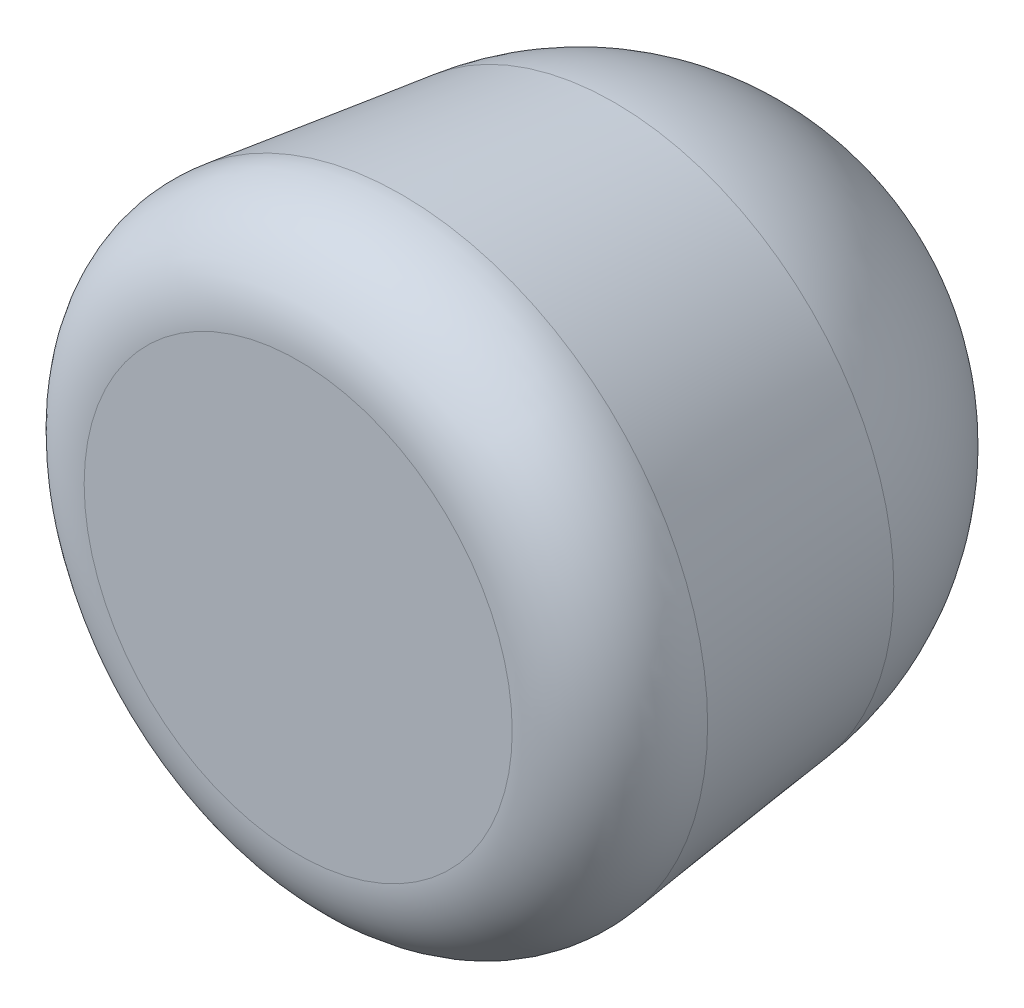
SolidWorks part; units mm, degrees
ref_plane "Front" through (0, 0, 0) normal (0, 0, 1) x (1, 0, 0)
ref_plane "Top" through (0, 0, 0) normal (0, 1, 0) x (1, 0, 0)
ref_plane "Right" through (0, 0, 0) normal (1, 0, 0) x (0, 0, -1)
sketch "Sketch1" plane through (0, 0, 0) normal (1, 0, 0) x (0, 0, -1)
  line L0 (18.6976, 151.2487) -> (-96.2656, 165.4606)
  line L1 (-152.4, 115.8383) -> (-152.4, 0)
  line L2 (0, 0) -> (152.4, 0) construction
  line L3 (152.4, 0) -> (-152.4, 0)
  arc A0 (-96.2656, 165.4606) -> (-152.4, 115.8383) centre (-102.4, 115.8383) ccw
  ellipse E0 centre (0, 0) end of major axis (0, 152.4) minor radius 152.4 (152.4, 0) -> (-152.4, 0) ccw
  point P17 (-152.4, 172.4)
  dimension "D4" = 50
  dimension "D1" = 304.8
  dimension "D2" = 304.8
  dimension "D3" = 172.4
revolve "Revolve1" add sketch "Sketch1" angle 360 about L2
equation "\"D3@Sketch1\"=\"D1@Sketch1\"/2+20"
